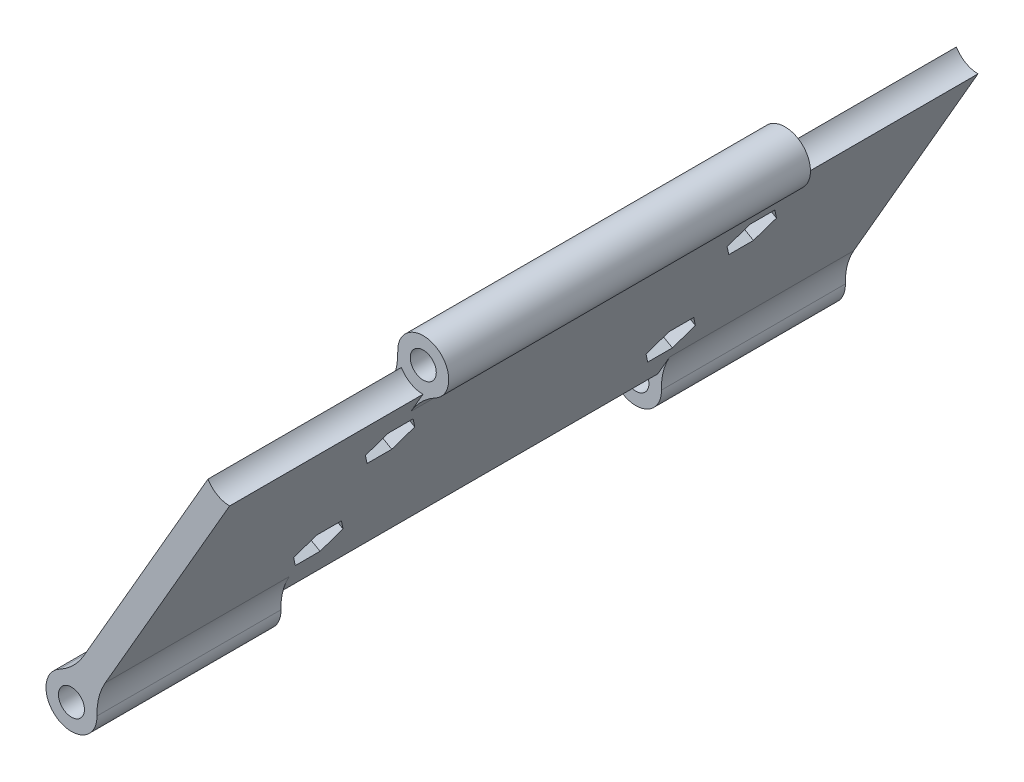
SolidWorks part; units mm, degrees
ref_plane "Front Plane" through (0, 0, 0) normal (0, 0, 1) x (1, 0, 0)
ref_plane "Top Plane" through (0, 0, 0) normal (0, 1, 0) x (1, 0, 0)
ref_plane "Right Plane" through (0, 0, 0) normal (1, 0, 0) x (0, 0, -1)
sketch "Sketch2" plane through (0, 0, 0) normal (0, 0, 1) x (1, 0, 0)
  line L0 (0, 0) -> (38.1, 0)
  line L1 (0, 0) -> (0, -38.1)
  circle A0 centre (0, 0) radius 38.1
  circle A1 centre (0, -29.337) radius 1.5875
  circle A2 centre (-25.4066, 14.6685) radius 1.5875
  circle A3 centre (25.4066, 14.6685) radius 1.5875
  point P13 (0, 0)
  dimension "D1" = 76.2
  dimension "D2" = 3.175
  dimension "D3" = 8.763
  dimension "D4" = 3
extrude "Boss-Extrude1" add sketch "Sketch2" along normal blind 10 contours A1 L1 L0 A0 A3 A2 | A1 L1 A0 L0
sketch "Sketch3" plane through (0, 0, 10) normal (0, 0, 1) x (1, 0, 0)
  line L1 (0, -29.337) -> (25.4066, 14.6685)
  line L2 (1.7321, -30.337) -> (27.1386, 13.6685)
  line L3 (-1.7321, -28.337) -> (23.6745, 15.6685)
  circle A11 centre (0, -29.337) radius 1.5875
  circle A12 centre (25.4066, 14.6685) radius 1.5875
  circle A17 centre (0, -29.337) radius 2.0875
  circle A18 centre (25.4066, 14.6685) radius 2.0875
  circle A19 centre (0, -29.337) radius 4.0875
  circle A20 centre (25.4066, 14.6685) radius 4.0875
  dimension "D1" = 0.5
  dimension "D2" = 2
  dimension "D4" = 2
  dimension "D5" = 2
extrude "Boss-Extrude2" add sketch "Sketch3" along normal blind 120 separate body contours L2 A20 L3 A18 | L1 A20 L2 A18 | L3 A20 L1 A18 | A20 L1 A19 L2 | A20 L3 A19 L1 | L1 A19 L3 A17 | L2 A19 L1 A17 | L3 A19 L2 A17
delete or keep bodies "Body-Delete/Keep 2" type delete bodies bodies 101
ref_plane "Plane1" through (0, 0, 70) normal (0, 0, 1) x (1, 0, 0)
sketch "Sketch4" plane through (0, 0, 70) normal (0, 0, 1) x (1, 0, 0)
  circle A1 centre (0, -29.337) radius 4.0875
extrude "Cut-Extrude1" cut sketch "Sketch4" against normal blind 30.5 and the other way blind 30.5
sketch "Sketch5" plane through (0, 0, 10) normal (0, 0, -1) x (-1, 0, 0)
  circle A0 centre (-25.4066, 14.6685) radius 4.0875
extrude "Cut-Extrude2" cut sketch "Sketch5" against normal offset from surface (31 mm away) 1.5 up to face at (2.0875, -29.337, 39.5) offset beyond the face yes
sketch "Sketch6" plane through (0, 0, 130) normal (0, 0, 1) x (1, 0, 0)
  circle A0 centre (25.4066, 14.6685) radius 4.0875
extrude "Cut-Extrude3" cut sketch "Sketch6" against normal offset from surface (31 mm away) 1.5 contours A0 up to face at (2.0875, -29.337, 100.5) offset beyond the face yes
fillet "Fillet1" radius 10 6 edges at (21.8921, 12.5813, 70) (0.0503, -25.2498, 24.75) (0.0503, -25.2498, 115.25) (3.5144, -27.2498, 115.25) (3.5144, -27.2498, 24.75) (25.3562, 10.5813, 70)
sketch "Sketch7" plane through (10.9712, -6.3343, 0) normal (-0.866, 0.5, 0) x (0, 0, 1)
  circle A0 centre (40.9814, 11.2661) radius 1.5
  circle A1 centre (42.4851, -11.7339) radius 1.5
  circle A2 centre (98.9814, -11.7339) radius 1.5
  circle A3 centre (98.9814, 11.2661) radius 1.5
  circle A4 centre (40.9814, 11.2661) radius 2
  circle A5 centre (42.4851, -11.7339) radius 2
  circle A6 centre (98.9814, -11.7339) radius 2
  circle A7 centre (98.9814, 11.2661) radius 2
  dimension "D1" = 0.5
extrude "Cut-Extrude4" cut sketch "Sketch7" against normal up to surface (4 mm away) contours A4 | A7 | A6 | A5 up to face at (14.7532, -7.7836, 70)
sketch "Sketch8" plane through (14.4353, -8.3343, 0) normal (0.866, -0.5, 0) x (0, 0, -1)
  line L1 (-37.0219, 11.2661) -> (-39.0016, 14.6951)
  line L2 (-39.0016, 14.6951) -> (-42.9611, 14.6951)
  line L3 (-42.9611, 14.6951) -> (-44.9408, 11.2661)
  line L4 (-44.9408, 11.2661) -> (-42.9611, 7.8371)
  line L5 (-42.9611, 7.8371) -> (-39.0016, 7.8371)
  line L6 (-39.0016, 7.8371) -> (-37.0219, 11.2661)
  line L7 (-38.5256, -11.7339) -> (-40.5053, -8.3049)
  line L8 (-40.5053, -8.3049) -> (-44.4648, -8.3049)
  line L9 (-44.4648, -8.3049) -> (-46.4445, -11.7339)
  line L10 (-46.4445, -11.7339) -> (-44.4648, -15.1629)
  line L11 (-44.4648, -15.1629) -> (-40.5053, -15.1629)
  line L12 (-40.5053, -15.1629) -> (-38.5256, -11.7339)
  line L13 (-95.0219, 11.2661) -> (-97.0016, 14.6951)
  line L14 (-97.0016, 14.6951) -> (-100.9611, 14.6951)
  line L15 (-100.9611, 14.6951) -> (-102.9408, 11.2661)
  line L16 (-102.9408, 11.2661) -> (-100.9611, 7.8371)
  line L17 (-100.9611, 7.8371) -> (-97.0016, 7.8371)
  line L18 (-97.0016, 7.8371) -> (-95.0219, 11.2661)
  line L19 (-95.0219, -11.7339) -> (-97.0016, -8.3049)
  line L20 (-97.0016, -8.3049) -> (-100.9611, -8.3049)
  line L21 (-100.9611, -8.3049) -> (-102.9408, -11.7339)
  line L22 (-102.9408, -11.7339) -> (-100.9611, -15.1629)
  line L23 (-100.9611, -15.1629) -> (-97.0016, -15.1629)
  line L24 (-97.0016, -15.1629) -> (-95.0219, -11.7339)
  circle A0 centre (-40.9814, 11.2661) radius 3.429 construction
  circle A1 centre (-42.4851, -11.7339) radius 3.429 construction
  circle A2 centre (-98.9814, 11.2661) radius 3.429 construction
  circle A3 centre (-98.9814, -11.7339) radius 3.429 construction
  dimension "D1" = 6.858
extrude "Cut-Extrude5" cut sketch "Sketch8" against normal blind 2
